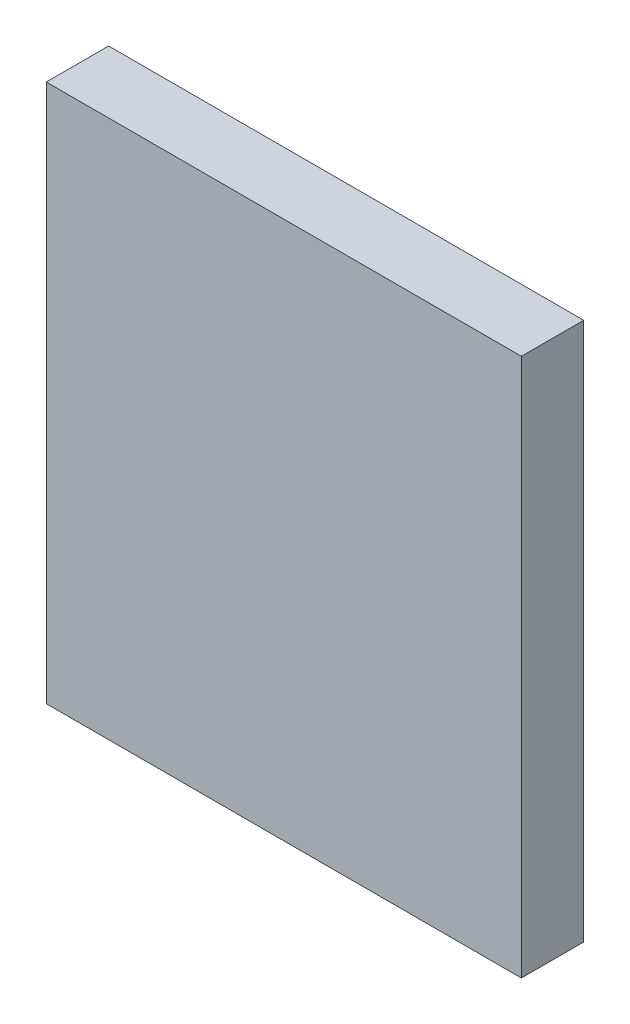
SolidWorks part; units mm, degrees
ref_plane "Front Plane" through (0, 0, 0) normal (0, 0, 1) x (1, 0, 0)
ref_plane "Top Plane" through (0, 0, 0) normal (0, 1, 0) x (1, 0, 0)
ref_plane "Right Plane" through (0, 0, 0) normal (1, 0, 0) x (0, 0, -1)
sketch "Sketch1" plane through (0, 0, 0) normal (0, 0, 1) x (1, 0, 0)
  line L0 (-3.81, 4.318) -> (3.81, 4.318)
  line L1 (3.81, 4.318) -> (3.81, -4.318)
  line L2 (3.81, -4.318) -> (-3.81, -4.318)
  line L3 (-3.81, -4.318) -> (-3.81, 4.318)
extrude "Component_Outline" add sketch "Sketch1" along normal blind 1 separate body
sketch3d "3DSketch1"
  line L0 (0, 0, 0) -> (1, 0, 0)
  line L1 (0, 0, 0) -> (0, 1, 0)
  line L2 (0, 0, 0) -> (0, 0, 1)
  point P0 (0, 0, 0)
